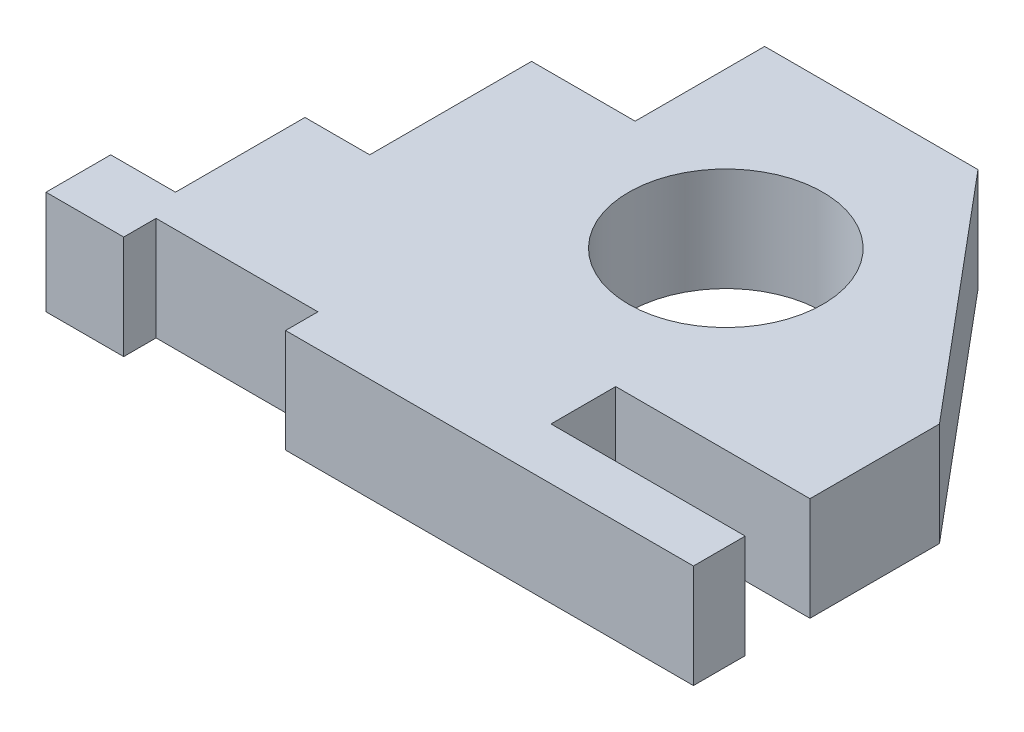
SolidWorks part; units mm, degrees
ref_plane "Front Plane" through (0, 0, 0) normal (0, 0, 1) x (1, 0, 0)
ref_plane "Top Plane" through (0, 0, 0) normal (0, 1, 0) x (1, 0, 0)
ref_plane "Right Plane" through (0, 0, 0) normal (1, 0, 0) x (0, 0, -1)
sketch "Sketch1" plane through (0, 0, 0) normal (0, 1, 0) x (1, 0, 0)
  line L0 (0, 0) -> (12, 0)
  line L1 (12, 0) -> (12, 5)
  line L2 (12, 5) -> (37, 5)
  line L3 (37, 5) -> (37, 0)
  line L4 (37, 0) -> (100, 0)
  line L5 (100, 0) -> (100, 8)
  line L6 (100, 8) -> (70, 8)
  line L7 (70, 8) -> (70, 18)
  line L8 (70, 18) -> (100, 18)
  line L9 (100, 18) -> (100, 38)
  line L10 (100, 38) -> (68.9533, 75)
  line L15 (0, 0) -> (0, 10)
  line L16 (0, 10) -> (10, 10)
  line L18 (10, 10) -> (10, 30)
  line L19 (10, 30) -> (20, 30)
  line L20 (20, 30) -> (20, 55)
  line L23 (68.9533, 75) -> (36, 75)
  line L24 (36, 75) -> (36, 55)
  line L25 (36, 55) -> (20, 55)
  circle A0 centre (60, 45) radius 15
  point P22 (0, 0)
  point P23 (0, 0)
  dimension "D18" = 30
  dimension "D1" = 38
  dimension "D2" = 10
  dimension "D3" = 8
  dimension "D4" = 30
  dimension "D5" = 100
  dimension "D6" = 25
  dimension "D7" = 5
  dimension "D8" = 10
  dimension "D9" = 40
  dimension "D10" = 75
  dimension "D11" = 30
  dimension "D12" = 55
  dimension "D13" = 10
  dimension "D14" = 20
  dimension "D15" = 36
  dimension "D16" = 30
  dimension "D17" = 12
  dimension "D19" = 45
  dimension "D20" = 40
extrude "Boss-Extrude1" add sketch "Sketch1" along normal blind 16
